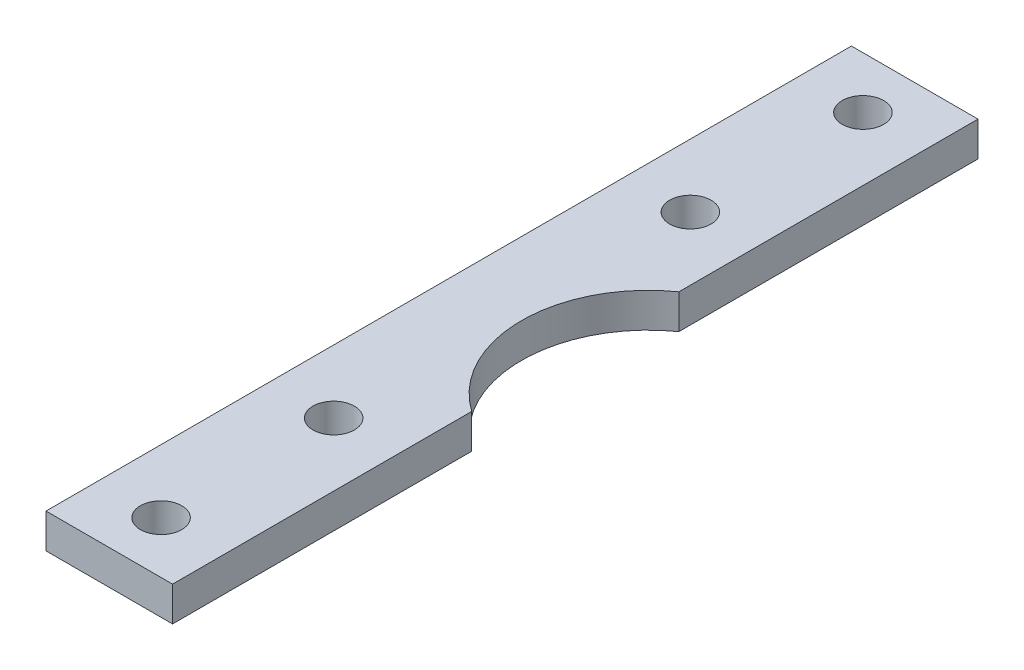
SolidWorks part; units mm, degrees
ref_plane "Front Plane" through (0, 0, 0) normal (0, 0, 1) x (1, 0, 0)
ref_plane "Top Plane" through (0, 0, 0) normal (0, 1, 0) x (1, 0, 0)
ref_plane "Right Plane" through (0, 0, 0) normal (1, 0, 0) x (0, 0, -1)
sketch "Sketch1" plane through (0, 0, 0) normal (0, 1, 0) x (1, 0, 0)
  line L0 (11, 44) -> (11, 70)
  line L1 (0, 0) -> (11, 0)
  line L2 (0, 0) -> (0, 70)
  line L3 (0, 70) -> (11, 70)
  line L4 (11, 0) -> (11, 26)
  circle A0 centre (5.5, 65.5) radius 1.8
  circle A1 centre (5.5, 4.5) radius 1.8
  circle A2 centre (5.5, 19.5) radius 1.8
  circle A3 centre (5.5, 50.5) radius 1.8
  arc A4 (11, 26) -> (11, 44) centre (17.3246, 35) cw
  point P10 (5.5, 70)
  point P12 (5.5, 0)
  point P18 (0, 35)
  point P19 (0, 0)
  point P20 (0, 0)
  point P21 (6.3246, 35)
  point P22 (0, 0)
  dimension "D3" = 3.6
  dimension "D4" = 3.6
  dimension "D6" = 4.5
  dimension "D7" = 3.6
  dimension "D8" = 3.6
  dimension "D11" = 11
  dimension "D1" = 70
  dimension "D2" = 11
  dimension "D5" = 61
  dimension "D9" = 15
  dimension "D10" = 15
  dimension "D12" = 18
extrude "Boss-Extrude1" add sketch "Sketch1" along normal blind 3
